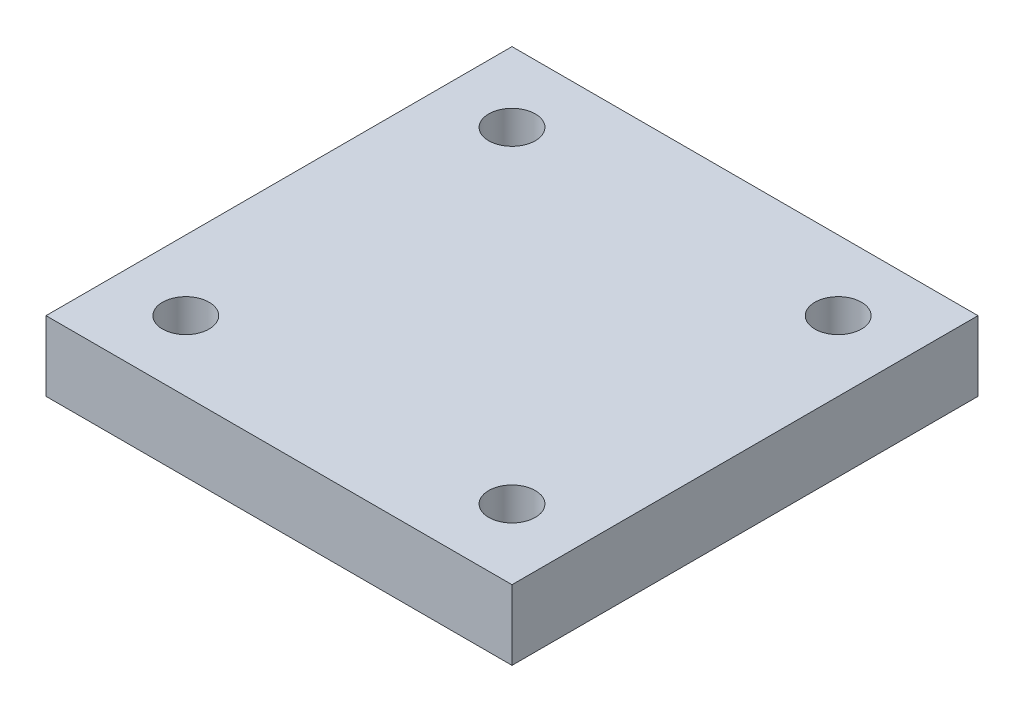
SolidWorks part; units mm, degrees
ref_plane "Front Plane" through (0, 0, 0) normal (0, 0, 1) x (1, 0, 0)
ref_plane "Top Plane" through (0, 0, 0) normal (0, 1, 0) x (1, 0, 0)
ref_plane "Right Plane" through (0, 0, 0) normal (1, 0, 0) x (0, 0, -1)
sketch "Sketch1" plane through (0, 0, 0) normal (0, 1, 0) x (1, 0, 0)
  circle A0 centre (0, 0) radius 6
  dimension "D1" = 12
extrude "Boss-Extrude1" add sketch "Sketch1" along normal blind 22
sketch "Sketch2" plane through (0, 22, 0) normal (0, 1, 0) x (1, 0, 0)
  line L1 (-50, 50) -> (50, 50)
  line L2 (-50, 50) -> (-50, -50)
  line L3 (-50, -50) -> (50, -50)
  line L4 (50, 50) -> (50, -50)
  line L5 (-50, 50) -> (50, -50) construction
  line L6 (-50, -50) -> (50, 50) construction
  line L11 (-35, 35) -> (35, -35) construction
  line L12 (-35, -35) -> (35, 35) construction
  circle A0 centre (-35, 35) radius 5
  circle A1 centre (35, 35) radius 5
  circle A2 centre (35, -35) radius 5
  circle A3 centre (-35, -35) radius 5
  point P0 (0, 0)
  point P6 (0, 0)
  dimension "D4" = 10
  dimension "D1" = 100
  dimension "D2" = 100
  dimension "D3" = 70
sketch "Sketch3" plane through (0, 22, 0) normal (0, 1, 0) x (1, 0, 0)
extrude "Boss-Extrude2" add sketch "Sketch2" along normal blind 15 contours A2 | A1 | A0 | A3 | L2 L3 L4 L1
